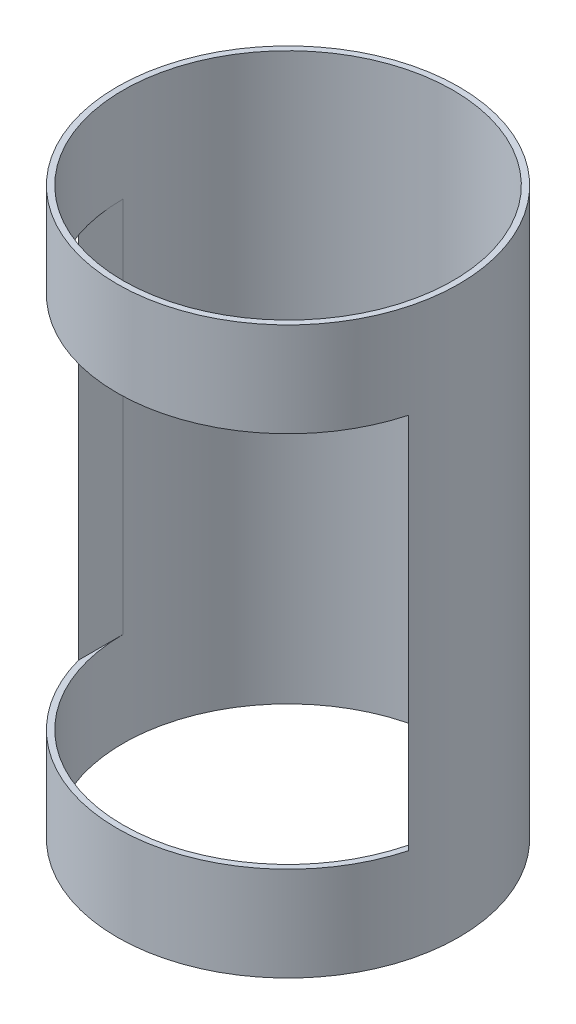
SolidWorks part; units mm, degrees
ref_plane "Front Plane" through (0, 0, 0) normal (0, 0, 1) x (1, 0, 0)
ref_plane "Top Plane" through (0, 0, 0) normal (0, 1, 0) x (1, 0, 0)
ref_plane "Right Plane" through (0, 0, 0) normal (1, 0, 0) x (0, 0, -1)
sketch "Sketch1" plane through (0, 0, 0) normal (0, 1, 0) x (1, 0, 0)
  circle A0 centre (0, 0) radius 88.9
  circle A1 centre (0, 0) radius 92.075
  dimension "D1" = 177.8
  dimension "D2" = 184.15
extrude "Boss-Extrude1" add sketch "Sketch1" along normal blind 304.8
sketch "Sketch2" plane through (0, 0, 0) normal (0, 0, 1) x (1, 0, 0)
  line L0 (0, 0) -> (0, 304.8) construction
  line L1 (88.9, 304.8) -> (-88.9, 304.8) construction
  line L2 (-92.075, 152.4) -> (92.075, 152.4) construction
  line L3 (-92.075, 304.8) -> (-92.075, 0) construction
  line L4 (92.075, 0) -> (92.075, 304.8) construction
  line L6 (-88.9, 50.8) -> (88.9, 50.8)
  line L7 (-88.9, 50.8) -> (-88.9, 254)
  line L8 (-88.9, 254) -> (88.9, 254)
  line L9 (88.9, 50.8) -> (88.9, 254)
  line L10 (-88.9, 50.8) -> (88.9, 254) construction
  line L11 (-88.9, 254) -> (88.9, 50.8) construction
  point P11 (0, 152.4)
  dimension "D1" = 177.8
  dimension "D2" = 203.2
extrude "Cut-Extrude1" cut sketch "Sketch2" along normal through all
